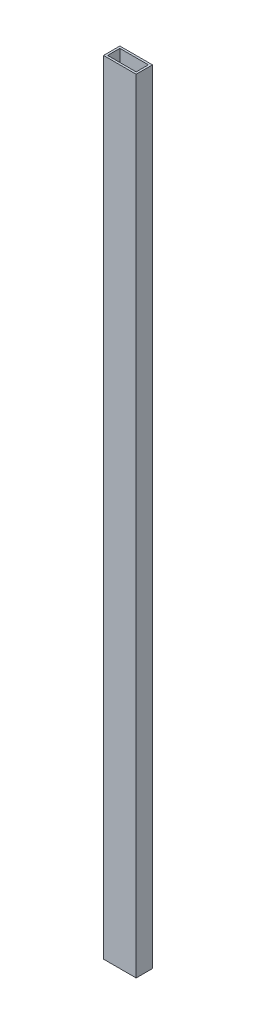
SolidWorks part; units mm, degrees
material "6061 Alloy"
ref_plane "Front Plane" through (0, 0, 0) normal (0, 0, 1) x (1, 0, 0)
ref_plane "Top Plane" through (0, 0, 0) normal (0, 1, 0) x (1, 0, 0)
ref_plane "Right Plane" through (0, 0, 0) normal (1, 0, 0) x (0, 0, -1)
sketch "Sketch1" plane through (0, 0, 0) normal (0, 1, 0) x (1, 0, 0)
  line L0 (-22.225, 9.525) -> (-22.225, 12.7) construction
  line L1 (-25.4, -12.7) -> (25.4, -12.7)
  line L2 (-25.4, -12.7) -> (-25.4, 12.7)
  line L3 (-25.4, 12.7) -> (25.4, 12.7)
  line L4 (25.4, -12.7) -> (25.4, 12.7)
  line L5 (-25.4, -12.7) -> (25.4, 12.7) construction
  line L6 (-25.4, 12.7) -> (25.4, -12.7) construction
  line L7 (-22.225, -9.525) -> (22.225, -9.525)
  line L8 (-22.225, -9.525) -> (-22.225, 9.525)
  line L9 (-22.225, 9.525) -> (22.225, 9.525)
  line L10 (22.225, -9.525) -> (22.225, 9.525)
  line L11 (-22.225, -9.525) -> (22.225, 9.525) construction
  line L12 (-22.225, 9.525) -> (22.225, -9.525) construction
  line L13 (-22.225, 9.525) -> (-25.4, 9.525) construction
  point P0 (0, 0)
  point P6 (0, 0)
  dimension "D1" = 3.175
  dimension "D2" = 50.8
  dimension "D3" = 25.4
extrude "Boss-Extrude1" add sketch "Sketch1" along normal blind 1219.2
sketch "Sketch2" [suppressed] plane through (0, 0, 12.7) normal (0, 0, 1) x (1, 0, 0)
  line L9 (-25.4, 0) -> (-25.4, 12.7)
  line L10 (-25.4, 1219.2) -> (-25.4, 0) construction
  line L11 (-25.4, 12.7) -> (-3.403, 0)
  line L12 (-25.4, 0) -> (25.4, 0) construction
  line L13 (-3.403, 0) -> (-25.4, 0)
  line L14 (25.4, 0) -> (-3.403, 0)
  line L15 (25.4, 0) -> (25.4, 49.8882)
  line L16 (25.4, 1219.2) -> (25.4, 0) construction
  line L17 (25.4, 49.8882) -> (-3.403, 0)
  line L18 (-25.4, 1219.2) -> (25.4, 1219.2) construction
  circle A0 centre (0, 1193.8) radius 19.05
  dimension "D3" = 38.1
  dimension "D1" = 30
  dimension "D2" = 25.4
  dimension "D4" = 38.1
extrude "Cut-Extrude1" [suppressed] cut sketch "Sketch2" against normal through all
